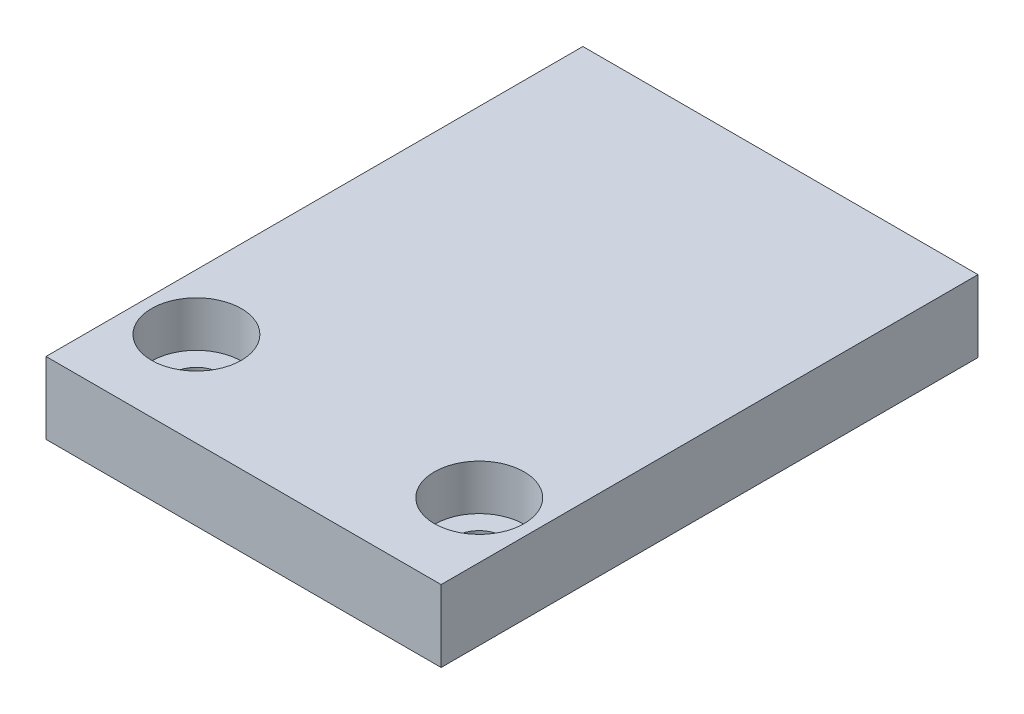
SolidWorks part; units mm, degrees
material "6061-T6 (SS)"
ref_plane "Front Plane" through (0, 0, 0) normal (0, 0, 1) x (1, 0, 0)
ref_plane "Top Plane" through (0, 0, 0) normal (0, 1, 0) x (1, 0, 0)
ref_plane "Right Plane" through (0, 0, 0) normal (1, 0, 0) x (0, 0, -1)
sketch "Sketch2" plane through (0, 0, 0) normal (0, 1, 0) x (1, 0, 0)
  line L1 (-20.955, -28.4738) -> (20.955, -28.4738)
  line L2 (-20.955, -28.4738) -> (-20.955, 28.4738)
  line L3 (-20.955, 28.4738) -> (20.955, 28.4738)
  line L4 (20.955, -28.4738) -> (20.955, 28.4738)
  line L5 (-20.955, -28.4738) -> (20.955, 28.4738) construction
  line L6 (-20.955, 28.4738) -> (20.955, -28.4738) construction
  point P0 (0, 0)
  dimension "D1" = 41.91
  dimension "D2" = 56.9476
extrude "Boss-Extrude1" add sketch "Sketch2" along normal blind 7.62
hole_wizard "CBORE for #10 Socket Head Cap Screw1" positions "Sketch3" profile "Sketch4" counterbore size "#10" standard "ANSI Inch" end condition through all
sketch "Sketch3" plane through (-20.955, 7.62, 28.4738) normal (0, 1, 0) x (-1, 0, 0)
  point P0 (-5.955, -10)
  point P1 (-35.955, -10)
sketch "Sketch4" plane through (-15, 7.62, 18.4738) normal (1, 0, 0) x (0, 0, 1)
  line L0 (0, 0) -> (0, 7.62)
  line L1 (0, 7.62) -> (2.5527, 7.62)
  line L2 (2.5527, 7.62) -> (2.5527, 4.826)
  line L3 (2.5527, 4.826) -> (4.7625, 4.826)
  line L4 (4.7625, 4.826) -> (4.7625, 0)
  line L5 (4.7625, 0) -> (0, 0)
  line L6 (0, -6.35) -> (0, 107.95) construction
  dimension "Thru Hole Dia." = 5.1054
  dimension "Thru Hole Depth" = 7.62
  dimension "C'Bore Dia." = 9.525
  dimension "C'Bore Depth" = 4.826
sketch "Sketch5" plane through (0, 0, 0) normal (0, -1, 0) x (1, 0, 0)
  line L1 (20.955, -28.4738) -> (-20.955, -28.4738) construction
  circle A0 centre (0, -13.2337) radius 4
  circle A1 centre (0, -13.2337) radius 4 construction
  point P2 (0, 0)
  point P4 (0, 0)
  point P6 (0, -28.4738)
